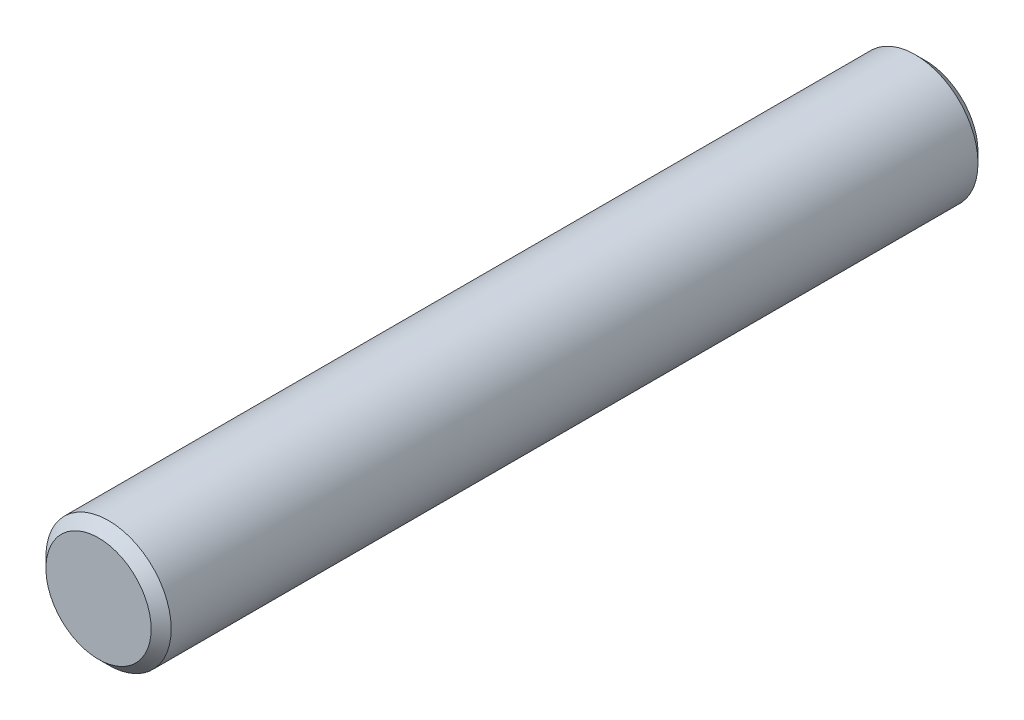
SolidWorks part; units mm, degrees
material "Plain Carbon Steel"
ref_plane "Front Plane" through (0, 0, 0) normal (0, 0, 1) x (1, 0, 0)
ref_plane "Top Plane" through (0, 0, 0) normal (0, 1, 0) x (1, 0, 0)
ref_plane "Right Plane" through (0, 0, 0) normal (1, 0, 0) x (0, 0, -1)
sketch "Sketch1" plane through (0, 0, 0) normal (0, 0, 1) x (1, 0, 0)
  circle A0 centre (0, 0) radius 2.5
  dimension "D1" = 5
extrude "Boss-Extrude1" add sketch "Sketch1" along normal blind 33
chamfer "Chamfer1" distance 0.4 angle 45 2 edges at (2.5, 0, 0) (2.5, 0, 33)
